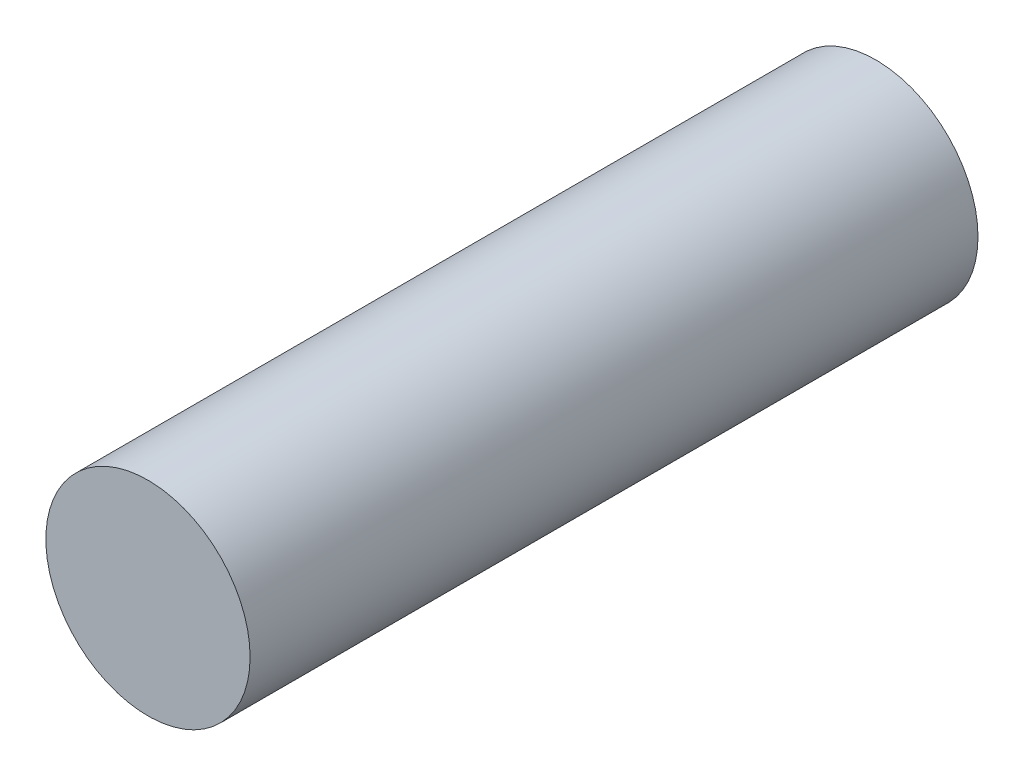
SolidWorks part; units mm, degrees
ref_plane "Front Plane" through (0, 0, 0) normal (0, 0, 1) x (1, 0, 0)
ref_plane "Top Plane" through (0, 0, 0) normal (0, 1, 0) x (1, 0, 0)
ref_plane "Right Plane" through (0, 0, 0) normal (1, 0, 0) x (0, 0, -1)
sketch "Sketch2" plane through (0, 0, 0) normal (0, 0, 1) x (1, 0, 0)
  circle A0 centre (0, 0) radius 1.375
  dimension "D1" = 2.75
extrude "Boss-Extrude1" add sketch "Sketch2" along normal blind 9.8
